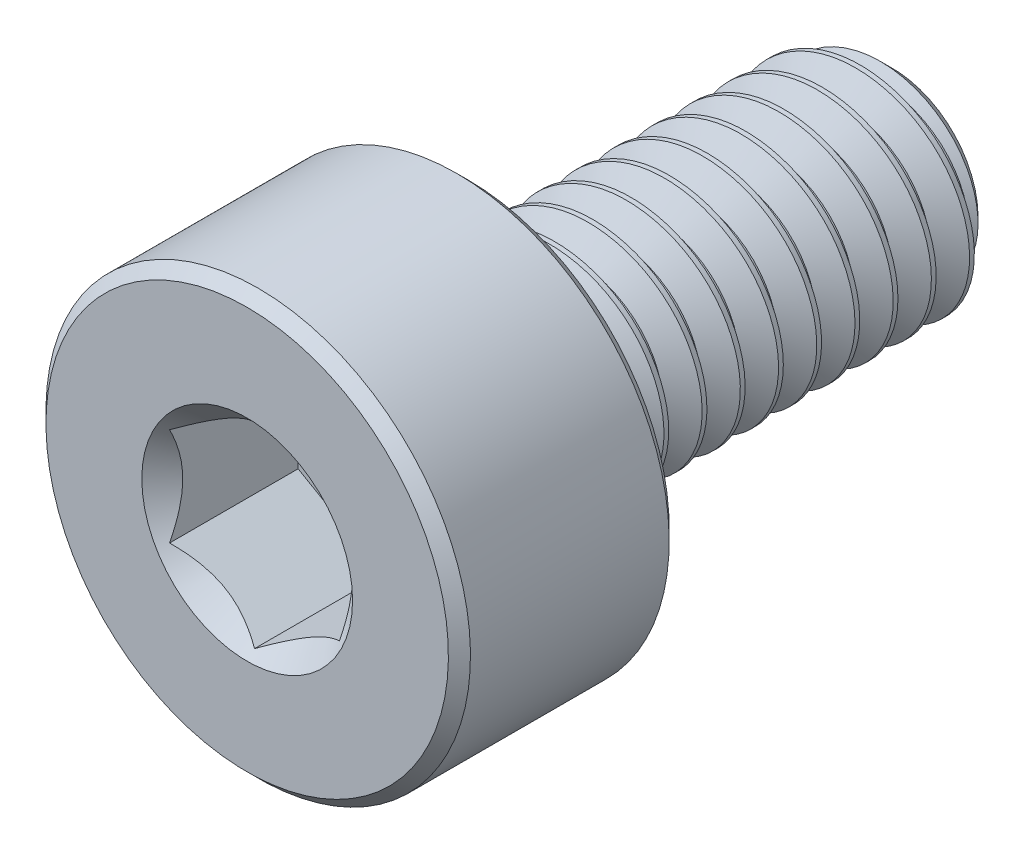
SolidWorks part; units mm, degrees
ref_plane "Front Plane" through (0, 0, 0) normal (0, 0, 1) x (1, 0, 0)
ref_plane "Top Plane" through (0, 0, 0) normal (0, 1, 0) x (1, 0, 0)
ref_plane "Right Plane" through (0, 0, 0) normal (1, 0, 0) x (0, 0, -1)
sketch "Sketch1" plane through (0, 0, 0) normal (1, 0, 0) x (0, 0, -1)
  line L0 (-3.8, 0) -> (3.8, 0) construction
  line L1 (3.8, 0) -> (3.8, 1.0077) construction
  line L2 (3.8, 1.0077) -> (3.5077, 1.3) construction
  line L3 (3.5077, 1.3) -> (3.4625, 1.3) construction
  line L4 (3.4625, 1.3) -> (-1.2, 1.3) construction
  line L5 (-1.2, 1.3) -> (-1.2, 2.5) construction
  line L6 (-1.2, 2.5) -> (-3.8, 2.5) construction
  line L7 (-3.8, 2.5) -> (-3.8, 0) construction
  line L8 (3.8, 1.0077) -> (3.8, 1.3) construction
  line L9 (3.7719, 1.3487) -> (3.9969, 0.959) construction
  line L10 (3.9969, 0.959) -> (4.2219, 1.3487) construction
  line L11 (4.2219, 1.3487) -> (3.7719, 1.3487) construction
  line L12 (3.9969, 1.3487) -> (3.9969, 1.3) construction
  line L13 (3.9969, 0.959) -> (3.9969, 1.0077) construction
  line L14 (3.9687, 1.0077) -> (4.025, 1.0077) construction
  line L15 (3.8, 1.3) -> (4.1938, 1.3) construction
  line L16 (3.7859, 1.3244) -> (4.2078, 1.3244) construction
  line L17 (3.8, 0) -> (3.8, -1.3) construction
  line L18 (-1.33, 2.5) -> (-1.2, 2.37) construction
  line L19 (-3.67, 2.5) -> (-3.8, 2.37) construction
  line L20 (-1.2, 1.3) -> (-1.2, 0) construction
  line L21 (-1.2, 0.65) -> (0.4667, 0.65) construction
  line L22 (0.4667, 0.65) -> (2.1333, 0.65) construction
  line L23 (2.1333, 0.65) -> (3.8, 0.65) construction
  line L24 (0.4667, 0.65) -> (0.4667, 1.3) construction
  line L25 (0.4667, 1.3) -> (0.4667, 2.5) construction
  line L26 (2.1333, 0.65) -> (2.1333, 2.5) construction
  point P0 (-3.8, 1)
  point P3 (2.675, 1.3)
  point P4 (0, 0)
  point P18 (2.1333, 1.3)
  point P22 (3.9969, 1.0077)
  point P24 (3.4625, 1.3)
  point P25 (3.9969, 1.3)
  point P28 (3.9969, 1.3244)
  point P29 (2.675, -1.3)
  point P30 (0.4667, 1.3)
  point P31 (-2.5, 2.5)
  point P37 (-1.655, 2.5)
  point P38 (-3.605, 2.5)
  point P45 (0.4667, 0.65)
  point P46 (2.1333, 0.65)
  dimension "D2" = 0.0563
  dimension "D7" = 0.13
  dimension "D8" = 0.13
  dimension "D9" = 0.13
  dimension "D10" = 0.065
  dimension "D11" = 0.325
  dimension "Drive Size" = 2
  dimension "Head Diameter" = 5
  dimension "Head Height" = 2.6
  dimension "Thread Pitch" = 0.45
  dimension "Thread Dia" = 2.6
  dimension "Length" = 5
  dimension "D12" = 0.3375
  dimension "D4" = 1.125
  dimension "D3" = 45
sketch "Sketch2" plane through (0, 0, 0) normal (1, 0, 0) x (0, 0, -1)
  line L0 (-3.8, 0) -> (-3.8, 2.37)
  line L1 (-3.67, 2.5) -> (-1.33, 2.5)
  line L2 (-1.2, 2.37) -> (-1.2, 1.43)
  line L4 (3.5077, 1.3) -> (3.8, 1.0077)
  line L5 (3.8, 1.0077) -> (3.8, 0)
  line L6 (-1.2, 2.5) -> (-3.8, 2.5) construction
  line L7 (3.8, 0) -> (-3.8, 0)
  line L8 (-3.67, 2.5) -> (-3.8, 2.37) construction
  line L10 (-3.67, 2.5) -> (-3.8, 2.37)
  line L14 (-1.33, 2.5) -> (-1.2, 2.37) construction
  line L16 (-1.33, 2.5) -> (-1.2, 2.37)
  line L17 (-1.2, 1.3) -> (-1.2, 2.5) construction
  line L19 (-1.07, 1.3) -> (3.5077, 1.3)
  line L20 (3.4625, 1.3) -> (-1.2, 1.3) construction
  arc A1 (-1.2, 1.43) -> (-1.07, 1.3) centre (-1.07, 1.43) ccw
  dimension "D3" = 0.13
revolve "Revolve1" add sketch "Sketch2" angle 360 about L7
sketch "Sketch3" plane through (0, 0, 3.8) normal (0, 0, 1) x (1, 0, 0)
  line L1 (1, -0.5774) -> (1, 0.5774)
  line L2 (1, 0.5774) -> (0, 1.1547)
  line L3 (0, 1.1547) -> (-1, 0.5774)
  line L4 (-1, 0.5774) -> (-1, -0.5774)
  line L5 (-1, -0.5774) -> (0, -1.1547)
  line L6 (0, -1.1547) -> (1, -0.5774)
  circle A0 centre (0, 0) radius 1 construction
  circle A1 centre (0, 0) radius 2.5 construction
  circle A2 centre (0, 0) radius 2.5 construction
  circle A3 centre (0, 0) radius 1.1547 construction
  point P13 (0, 0)
  dimension "D1" = 2.3094
extrude "Cut-Extrude1" cut sketch "Sketch3" against normal offset from surface (1.6 mm away) 1 up to face at (0, 2.37, 1.2)
sketch "Sketch4" plane through (0, 0, 3.8) normal (0, 0, 1) x (1, 0, 0)
  circle A0 centre (0, 0) radius 1.2413
  dimension "D1" = 2.4826
extrude "Cut-Extrude2" cut sketch "Sketch4" against normal up to vertex (1.3 mm away) draft 45 up to point (0, 2.5, 2.5)
sketch "Sketch11" plane through (0, 0, 0) normal (1, 0, 0) x (0, 0, -1)
  line L0 (-3.8, 0) -> (3.8, 0) construction
  line L1 (-3.8, 0) -> (3.8, 0) construction
  line L2 (-0.2625, 0) -> (-0.2625, 1.3) construction
  line L3 (3.4625, 1.3) -> (-1.2, 1.3) construction
  line L4 (2.8625, 0) -> (2.8625, 1.3) construction
  line L6 (3.8, 1.0077) -> (3.8, 1.3) construction
  point P2 (-0.2625, 0)
  point P3 (2.8625, 0)
  dimension "D1" = 0.9375
  dimension "D2" = 0.9375
sketch "Sketch6" plane through (0, 0, -3.8) normal (0, 0, -1) x (-1, 0, 0)
  circle A0 centre (0, 0) radius 1.3
curve "Helix/Spiral1" pitch 0.45 height 5.45 turns 12.1111
sketch "Sketch10" plane through (0, 0, 0) normal (1, 0, 0) x (0, 0, -1)
  line L0 (-1.07, -2.5) -> (-1.07, 2.5)
  line L5 (-3.8, 0) -> (3.8, 0) construction
  line L6 (-1.07, 1.3) -> (-1.07, -1.3) construction
  point P3 (-1.07, 0)
split "Split1" trim tools "Sketch10" bodies to split 106 resulting bodies 114 115
sketch "Sketch7" plane through (0, 0, 0) normal (1, 0, 0) x (0, 0, -1)
  line L0 (3.7859, 1.3244) -> (4.2078, 1.3244)
  line L1 (4.2078, 1.3244) -> (4.025, 1.0077)
  line L2 (4.025, 1.0077) -> (3.9687, 1.0077)
  line L3 (3.9687, 1.0077) -> (3.7859, 1.3244)
sweep "Cut-Sweep1" cut profiles "Sketch7" path "Helix/Spiral1"
sketch "Sketch8" plane through (0, 0, 0) normal (1, 0, 0) x (0, 0, -1)
  line L0 (-1.2, 0) -> (-1.2, 1.3)
  line L1 (-1.07, -1.3) -> (-1.07, 1.3) construction
  line L2 (-1.2, 1.3) -> (-1.07, 1.3)
  line L4 (-1.07, 1.3) -> (-0.3194, 0)
  line L5 (-0.3194, 0) -> (-1.2, 0)
  line L6 (3.4625, 1.3) -> (-1.2, 1.3) construction
  line L7 (-3.8, 0) -> (3.8, 0) construction
  dimension "D1" = 60
revolve "Revolve2" add sketch "Sketch8" angle 360 about L5
equation "\"D2@Sketch1\" = \"Thread Pitch@Sketch1\" / 8"
equation "\"D4@Helix/Spiral1\" = \"Thread Pitch@Sketch1\""
equation "\"D7@Sketch1\" = \"Head Height@Sketch1\" * .05"
equation "\"D8@Sketch1\"=\"D7@Sketch1\""
equation "\"D9@Sketch1\"=\"D7@Sketch1\""
equation "\"D10@Sketch1\"=\"D7@Sketch1\"/2"
equation "\"D11@Sketch1\"=\"D10@Sketch1\"*5"
equation "\"D4@Sketch1\"=\"Thread Pitch@Sketch1\"*2.5"
equation "\"D12@Sketch1\"=\"Thread Pitch@Sketch1\"*.75"
equation "\"D3@Helix/Spiral1\"=\"Length@Sketch1\"+\"Thread Pitch@Sketch1\""
equation "\"D3@Sketch2\"=\"Thread Dia@Sketch1\"*0.05"
equation "\"D1@Sketch11\"=\"Length@Sketch1\"*0.1875"
equation "\"D2@Sketch11\"=\"D1@Sketch11\""
equation "\"D1@Sketch4\"=\"D1@Sketch3\"*1.075"
